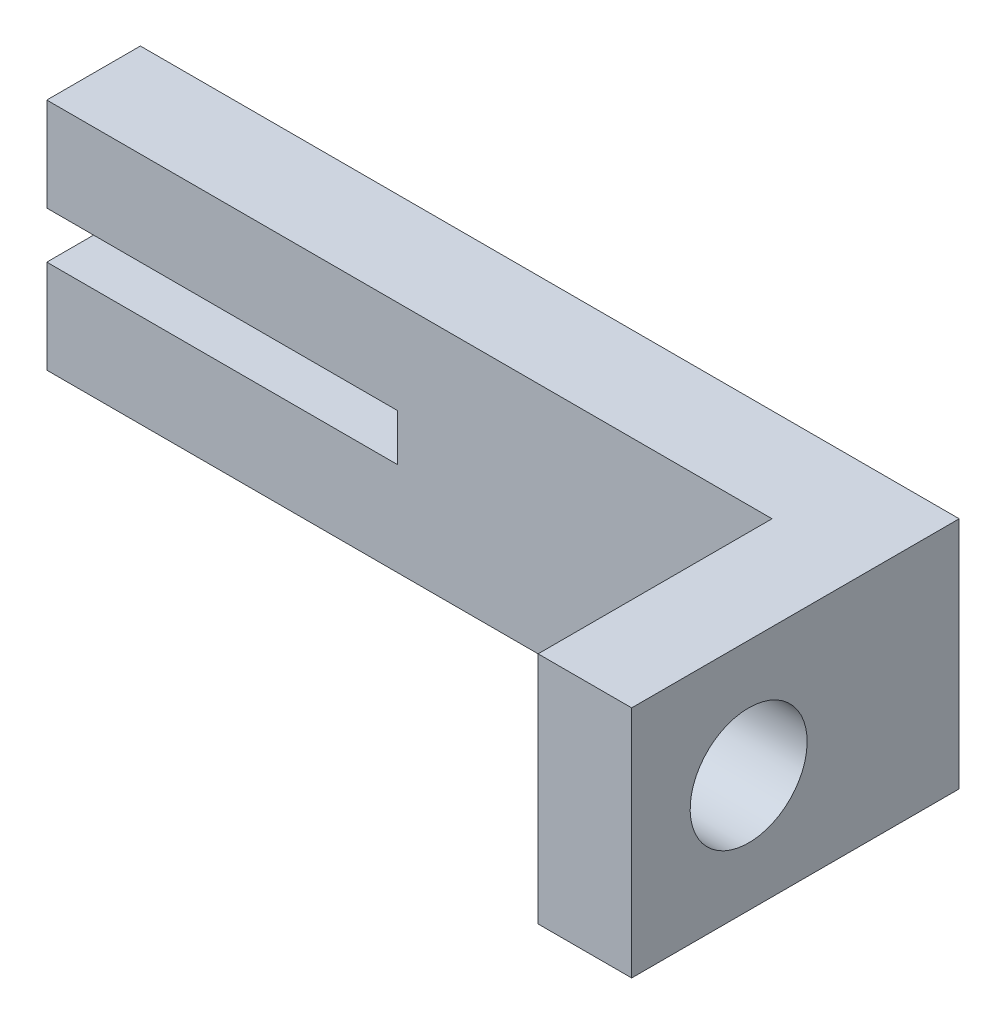
SolidWorks part; units mm, degrees
ref_plane "Front Plane" through (0, 0, 0) normal (0, 0, 1) x (1, 0, 0)
ref_plane "Top Plane" through (0, 0, 0) normal (0, 1, 0) x (1, 0, 0)
ref_plane "Right Plane" through (0, 0, 0) normal (1, 0, 0) x (0, 0, -1)
sketch "Sketch1" plane through (0, 0, 0) normal (0, 0, 1) x (1, 0, 0)
  line L0 (15, 10) -> (15, 0)
  line L1 (0, 0) -> (35, 0)
  line L2 (0, 0) -> (0, 10)
  line L3 (0, 10) -> (35, 10)
  line L4 (35, 0) -> (35, 10)
  line L6 (0, 6) -> (15, 6)
  line L7 (0, 6) -> (0, 4)
  line L8 (0, 4) -> (15, 4)
  line L9 (15, 6) -> (15, 4)
  dimension "D1" = 10
  dimension "D2" = 35
  dimension "D3" = 20
  dimension "D4" = 4
  dimension "D5" = 2
extrude "Boss-Extrude1" add sketch "Sketch1" along normal blind 4 contours L2 L6 L0 L3 | L1 L4 L3 L0 | L8 L2 L1 L0
sketch "Sketch2" plane through (0, 0, 4) normal (0, 0, 1) x (1, 0, 0)
  line L0 (0, 0) -> (35, 0) construction
  line L1 (35, 10) -> (31, 10)
  line L2 (35, 10) -> (35, 0)
  line L3 (35, 0) -> (31, 0)
  line L4 (31, 10) -> (31, 0)
  dimension "D1" = 4
extrude "Boss-Extrude2" add sketch "Sketch2" along normal blind 10 contours L2 L1 L4 L3
sketch "Sketch3" plane through (35, 0, 0) normal (1, 0, 0) x (0, 0, -1)
  line L0 (-14, 10) -> (0, 10) construction
  line L1 (-14, 10) -> (-14, 0) construction
  circle A0 centre (-9, 5) radius 2.5
  dimension "D3" = 5
  dimension "D1" = 5
  dimension "D2" = 5
extrude "Cut-Extrude1" cut sketch "Sketch3" against normal blind 10 contours A0
